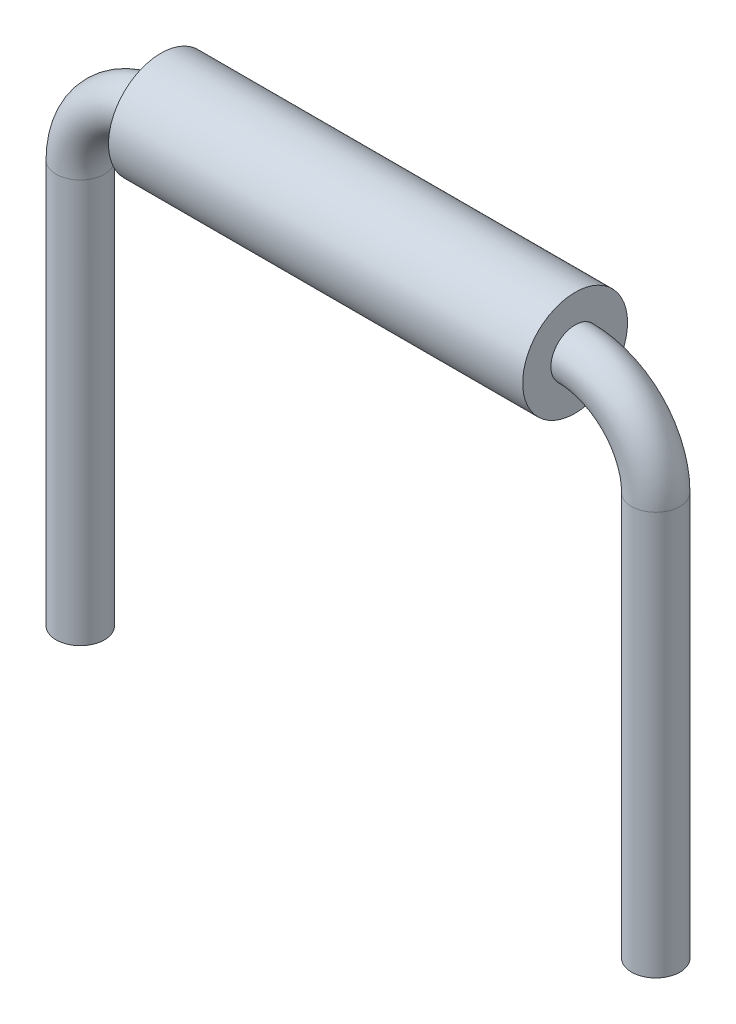
SolidWorks part; units mm, degrees
other "Wire"
other "Insulation"
ref_plane "Front Plane" through (0, 0, 0) normal (0, 0, 1) x (1, 0, 0)
ref_plane "Top Plane" through (0, 0, 0) normal (0, 1, 0) x (1, 0, 0)
ref_plane "Right Plane" through (0, 0, 0) normal (1, 0, 0) x (0, 0, -1)
sketch "Sketch1" plane through (0, 0, 0) normal (0, 0, 1) x (1, 0, 0)
  line L0 (-2.5675, 0) -> (2.5675, 0)
  line L1 (-3.5675, -1) -> (-3.5675, -6)
  line L2 (3.5675, -1) -> (3.5675, -6)
  line L3 (0, 0) -> (0, -6) construction
  line L4 (-3.5675, -6) -> (3.5675, -6) construction
  arc A0 (-2.5675, 0) -> (-3.5675, -1) centre (-2.5675, -1) ccw
  arc A1 (2.5675, 0) -> (3.5675, -1) centre (2.5675, -1) cw
  dimension "D1" = 1
  dimension "D2" = 7.135
  dimension "D3" = 6
sketch "Sketch2" plane through (0, 0, 0) normal (1, 0, 0) x (0, 0, -1)
  circle A0 centre (0, 0) radius 0.3
  dimension "D1" = 0.6
sweep "Sweep1" add profiles "Sketch2" path "Sketch1"
sketch "Sketch3" plane through (0, 0, 0) normal (1, 0, 0) x (0, 0, -1)
  circle A0 centre (0, 0) radius 0.65
  circle A1 centre (0, 0) radius 0.3
  dimension "D1" = 1.3
  dimension "D2" = 0.6
extrude "Boss-Extrude1" add sketch "Sketch3" along normal up to vertex (2.5675 mm away) and the other way up to vertex (2.5675 mm away) separate body up to point (2.5675, 0, 0) other way up to point (-2.5675, 0, 0)
